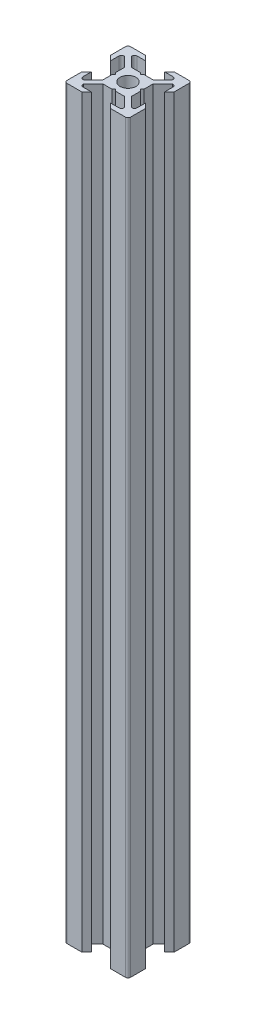
SolidWorks part; units mm, degrees
ref_plane "Face" through (0, 0, 0) normal (0, 0, 1) x (1, 0, 0)
ref_plane "Dessus" through (0, 0, 0) normal (0, 1, 0) x (1, 0, 0)
ref_plane "Droite" through (0, 0, 0) normal (1, 0, 0) x (0, 0, -1)
sketch "Esquisse1" plane through (0, 0, 0) normal (0, 1, 0) x (1, 0, 0)
  line L0 (0, 0) -> (0, 10) construction
  line L1 (0, 0) -> (-10, 0) construction
  line L2 (-10, 0) -> (-10, 10) construction
  line L3 (-10, 10) -> (0, 10) construction
  line L4 (0, 4) -> (-0.5, 4.5)
  line L5 (-0.5, 4.5) -> (-3.4393, 4.5)
  line L6 (-3.4393, 4.5) -> (-6.4393, 7.5)
  line L7 (-6.4393, 7.5) -> (-6.4393, 8.5)
  line L8 (-6.4393, 8.5) -> (-3, 8.5)
  line L9 (-3, 8.5) -> (-4.5, 10)
  line L10 (-4.5, 10) -> (-10, 10)
  line L11 (0, 0) -> (-10, 10) construction
  line L12 (-10, 4.5) -> (-10, 10)
  line L13 (-8.5, 3) -> (-10, 4.5)
  line L14 (-8.5, 6.4393) -> (-8.5, 3)
  line L15 (-7.5, 6.4393) -> (-8.5, 6.4393)
  line L16 (-4.5, 3.4393) -> (-7.5, 6.4393)
  line L17 (-4.5, 0.5) -> (-4.5, 3.4393)
  line L18 (-4, 0) -> (-4.5, 0.5)
  line L19 (0, -4) -> (-0.5, -4.5)
  line L20 (-0.5, -4.5) -> (-3.4393, -4.5)
  line L21 (-4, 0) -> (-4.5, -0.5)
  line L22 (-4.5, -0.5) -> (-4.5, -3.4393)
  line L23 (-4.5, -3.4393) -> (-7.5, -6.4393)
  line L24 (-3.4393, -4.5) -> (-6.4393, -7.5)
  line L25 (-3, -8.5) -> (-4.5, -10)
  line L26 (-6.4393, -8.5) -> (-3, -8.5)
  line L27 (-6.4393, -7.5) -> (-6.4393, -8.5)
  line L28 (-7.5, -6.4393) -> (-8.5, -6.4393)
  line L29 (-4.5, -10) -> (-10, -10)
  line L30 (-10, -4.5) -> (-10, -10)
  line L31 (-8.5, -3) -> (-10, -4.5)
  line L32 (-8.5, -6.4393) -> (-8.5, -3)
  line L33 (8.5, -6.4393) -> (8.5, -3)
  line L34 (8.5, -3) -> (10, -4.5)
  line L35 (10, -4.5) -> (10, -10)
  line L36 (4.5, -10) -> (10, -10)
  line L37 (7.5, -6.4393) -> (8.5, -6.4393)
  line L38 (6.4393, -7.5) -> (6.4393, -8.5)
  line L39 (6.4393, -8.5) -> (3, -8.5)
  line L40 (3, -8.5) -> (4.5, -10)
  line L41 (3.4393, -4.5) -> (6.4393, -7.5)
  line L42 (4.5, -3.4393) -> (7.5, -6.4393)
  line L43 (4.5, -0.5) -> (4.5, -3.4393)
  line L44 (4, 0) -> (4.5, -0.5)
  line L45 (0.5, -4.5) -> (3.4393, -4.5)
  line L46 (0, -4) -> (0.5, -4.5)
  line L47 (4, 0) -> (4.5, 0.5)
  line L48 (4.5, 0.5) -> (4.5, 3.4393)
  line L49 (4.5, 3.4393) -> (7.5, 6.4393)
  line L50 (7.5, 6.4393) -> (8.5, 6.4393)
  line L51 (8.5, 6.4393) -> (8.5, 3)
  line L52 (8.5, 3) -> (10, 4.5)
  line L53 (10, 4.5) -> (10, 10)
  line L54 (4.5, 10) -> (10, 10)
  line L55 (3, 8.5) -> (4.5, 10)
  line L56 (6.4393, 8.5) -> (3, 8.5)
  line L57 (6.4393, 7.5) -> (6.4393, 8.5)
  line L58 (3.4393, 4.5) -> (6.4393, 7.5)
  line L59 (0.5, 4.5) -> (3.4393, 4.5)
  line L60 (0, 4) -> (0.5, 4.5)
  circle A0 centre (0, 0) radius 2.5
  dimension "D10" = 5
  dimension "D1" = 10
  dimension "D2" = 45
  dimension "D3" = 45
  dimension "D4" = 1.5
  dimension "D5" = 7
  dimension "D6" = 1
  dimension "D7" = 4.5
  dimension "D8" = 0.5
  dimension "D9" = 0.75
extrude "Extrusion1" add sketch "Esquisse1" along normal blind 234.5
fillet "Congé1" radius 0.75 12 edges at (-8.5, 117.25, -6.4393) (-6.4393, 117.25, -8.5) (8.5, 117.25, -6.4393) (6.4393, 117.25, -8.5) (-8.5, 117.25, 6.4393) (-6.4393, 117.25, 8.5) (8.5, 117.25, 6.4393) (6.4393, 117.25, 8.5) (10, 117.25, -10) (-10, 117.25, -10) (-10, 117.25, 10) (10, 117.25, 10)
